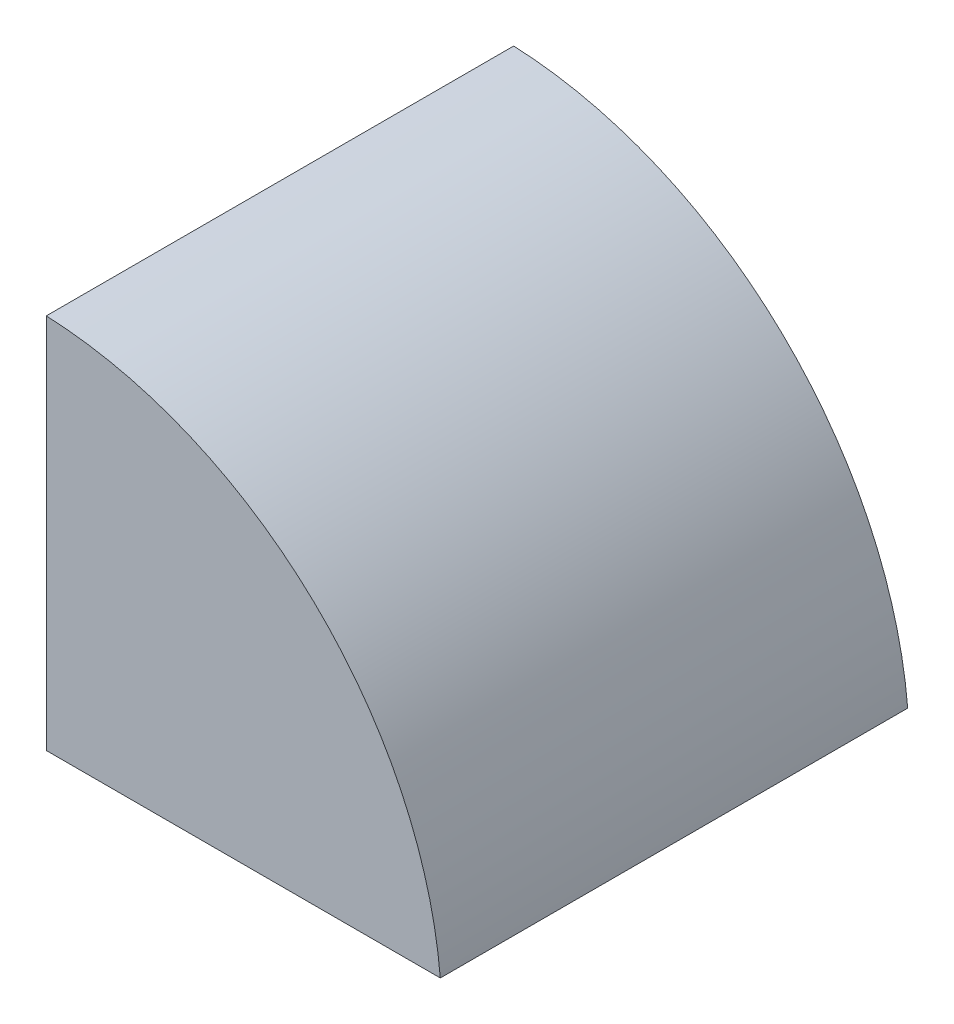
SolidWorks part; units mm, degrees
material "St3S"
ref_plane "Płaszczyzna przednia" through (0, 0, 0) normal (0, 0, 1) x (1, 0, 0)
ref_plane "Płaszczyzna górna" through (0, 0, 0) normal (0, 1, 0) x (1, 0, 0)
ref_plane "Płaszczyzna prawa" through (0, 0, 0) normal (1, 0, 0) x (0, 0, -1)
sketch "Szkic1" plane through (0, 0, 0) normal (0, 0, 1) x (1, 0, 0)
  line L1 (1.1492, 2.3576) -> (26.4392, 2.3576)
  line L2 (1.1492, 2.3576) -> (1.1492, 26.5192)
  arc A0 (26.4392, 2.3576) -> (1.1492, 26.5192) centre (0, 0) ccw
extrude "Dodanie-wyciągnięcie1" add sketch "Szkic1" along normal blind 30
pattern_circular "Szyk kołowy1" count 4 over 360 about axis through (0, 0, 30) along (0, 0, -1) of "Dodanie-wyciągnięcie1"
